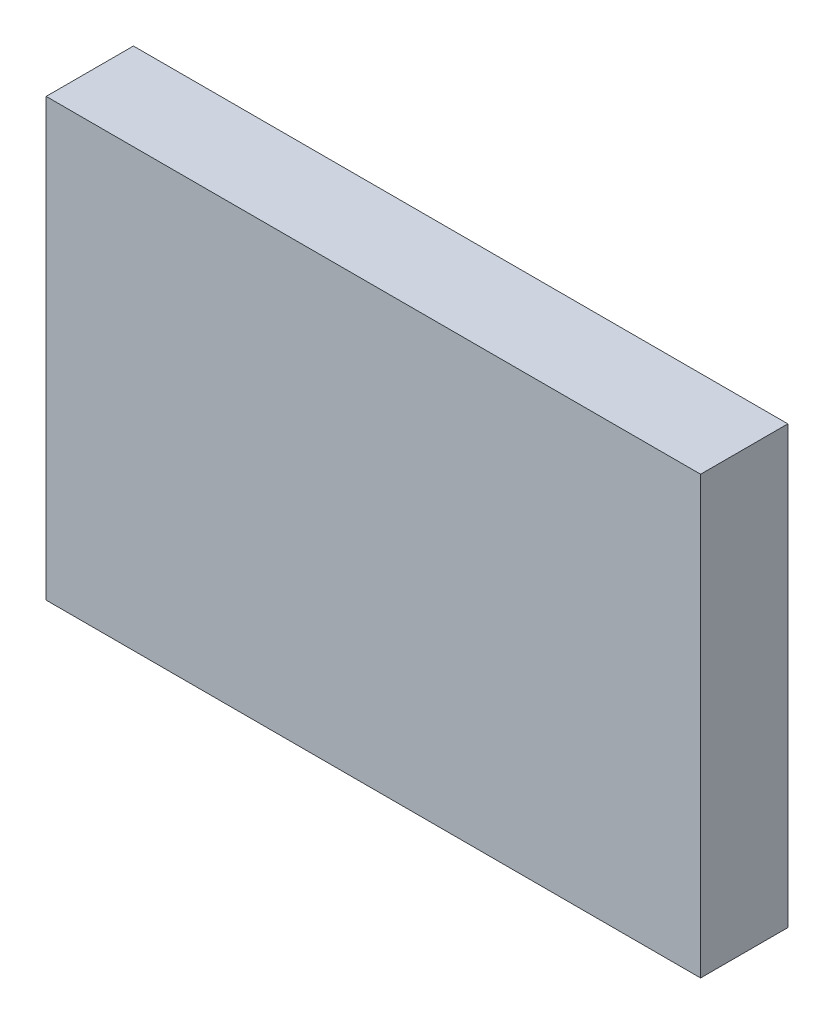
SolidWorks part; units mm, degrees
material "1023 Листовая углеродистая сталь (SS)"
ref_plane "Front" through (0, 0, 0) normal (0, 0, 1) x (1, 0, 0)
ref_plane "Top" through (0, 0, 0) normal (0, 1, 0) x (1, 0, 0)
ref_plane "Right" through (0, 0, 0) normal (1, 0, 0) x (0, 0, -1)
sketch "Sketch1" plane through (0, 0, 0) normal (0, 0, 1) x (1, 0, 0)
  line L1 (-75, 50) -> (75, 50)
  line L2 (-75, 50) -> (-75, -50)
  line L3 (-75, -50) -> (75, -50)
  line L4 (75, 50) -> (75, -50)
  line L5 (-75, 50) -> (75, -50) construction
  line L6 (-75, -50) -> (75, 50) construction
  point P0 (0, 0)
  dimension "D1" = 100
  dimension "D2" = 150
extrude "Extrude1" add sketch "Sketch1" along normal blind 20
